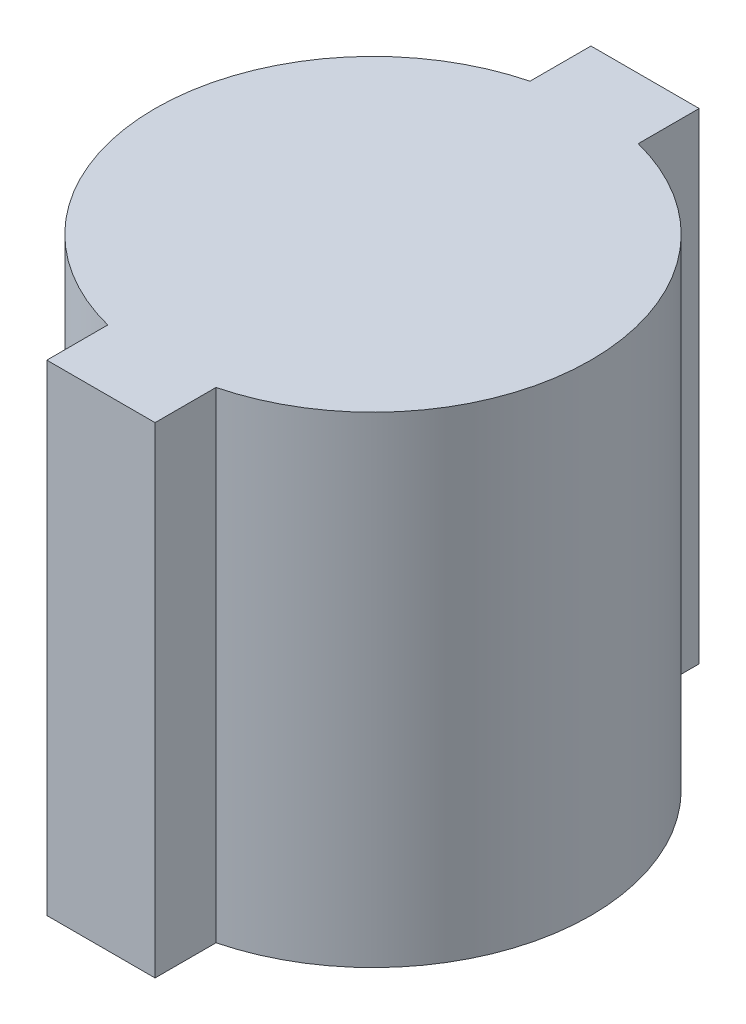
SolidWorks part; units mm, degrees
ref_plane "Front Plane" through (0, 0, 0) normal (0, 0, 1) x (1, 0, 0)
ref_plane "Top Plane" through (0, 0, 0) normal (0, 1, 0) x (1, 0, 0)
ref_plane "Right Plane" through (0, 0, 0) normal (1, 0, 0) x (0, 0, -1)
sketch "Sketch1" plane through (0, 0, 0) normal (0, 1, 0) x (1, 0, 0)
  line L1 (-2.286, 6.9215) -> (2.286, 6.9215)
  line L2 (-2.286, 6.9215) -> (-2.286, 11.4935)
  line L3 (-2.286, 11.4935) -> (2.286, 11.4935)
  line L4 (2.286, 6.9215) -> (2.286, 11.4935)
  line L5 (-2.286, 6.9215) -> (2.286, 11.4935) construction
  line L6 (-2.286, 11.4935) -> (2.286, 6.9215) construction
  line L7 (-2.286, -11.4935) -> (2.286, -11.4935)
  line L8 (-2.286, -11.4935) -> (-2.286, -6.9215)
  line L9 (-2.286, -6.9215) -> (2.286, -6.9215)
  line L10 (2.286, -11.4935) -> (2.286, -6.9215)
  line L11 (-2.286, -11.4935) -> (2.286, -6.9215) construction
  line L12 (-2.286, -6.9215) -> (2.286, -11.4935) construction
  circle A0 centre (0, 0) radius 9.2075
  point P3 (0, 9.2075)
  point P8 (0, -9.2075)
  dimension "D1" = 18.415
  dimension "D2" = 4.572
  dimension "D3" = 4.572
  dimension "D4" = 4.572
  dimension "D5" = 4.572
extrude "Boss-Extrude1" add sketch "Sketch1" along normal blind 20.32 contours A0 L4 L3 L2 | L4 A0 L2 L1 | L10 A0 L4 L1 L2 L8 L9 | L8 A0 L10 L9 | A0 L8 L7 L10
